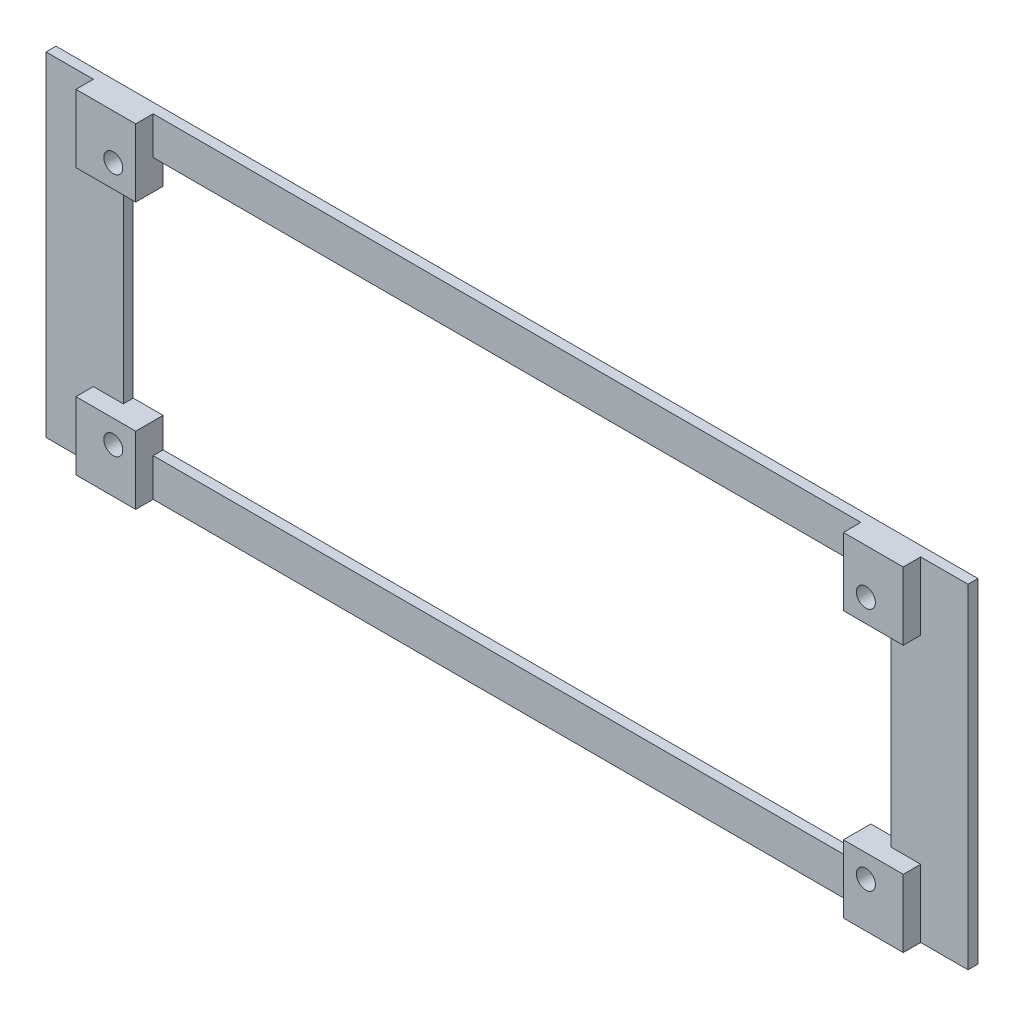
SolidWorks part; units mm, degrees
ref_plane "Přední rovina" through (0, 0, 0) normal (0, 0, 1) x (1, 0, 0)
ref_plane "Horní rovina" through (0, 0, 0) normal (0, 1, 0) x (1, 0, 0)
ref_plane "Pravá rovina" through (0, 0, 0) normal (1, 0, 0) x (0, 0, -1)
sketch "Skica1" plane through (0, 0, 0) normal (0, 0, 1) x (1, 0, 0)
  line L0 (-71, -25.9) -> (-71, -19.9)
  line L1 (-92.5, 33.5) -> (92.5, 33.5)
  line L2 (-92.5, 33.5) -> (-92.5, -33.5)
  line L3 (-92.5, -33.5) -> (92.5, -33.5)
  line L4 (92.5, 33.5) -> (92.5, -33.5)
  line L5 (-92.5, 33.5) -> (92.5, -33.5) construction
  line L6 (-92.5, -33.5) -> (92.5, 33.5) construction
  line L7 (-77, 25.9) -> (77, 25.9)
  line L8 (-77, 25.9) -> (-77, -25.9)
  line L9 (-77, -25.9) -> (77, -25.9)
  line L10 (77, 25.9) -> (77, -25.9)
  line L11 (-77, 25.9) -> (77, -25.9) construction
  line L12 (-77, -25.9) -> (77, 25.9) construction
  line L13 (-71, -19.9) -> (-77, -19.9)
  line L14 (0, 0) -> (0, -11.7122)
  line L15 (0, 0) -> (-11.7427, 0)
  line L16 (-71, 25.9) -> (-71, 19.9)
  line L17 (-71, 19.9) -> (-77, 19.9)
  line L18 (71, -25.9) -> (71, -19.9)
  line L19 (71, -19.9) -> (77, -19.9)
  line L20 (71, 25.9) -> (71, 19.9)
  line L21 (71, 19.9) -> (77, 19.9)
  point P0 (0, 0)
  point P6 (0, 0)
  dimension "D1" = 185
  dimension "D2" = 67
  dimension "D3" = 154
  dimension "D4" = 51.8
  dimension "D5" = 6
  dimension "D6" = 6
extrude "Přidat vysunutím1" add sketch "Skica1" along normal blind 2 contours L4 L1 L2 L3 L7 L10 L9 L8 | L17 L16 L7 L8 | L0 L13 L8 L9 | L19 L18 L9 L10 | L20 L21 L10 L7
sketch "Skica2" plane through (0, 0, 2) normal (0, 0, 1) x (1, 0, 0)
  line L0 (71, 19.9) -> (83, 19.9)
  line L1 (83, 19.9) -> (83, 33.5)
  line L2 (83, 33.5) -> (71, 33.5)
  line L3 (71, 33.5) -> (71, 19.9)
  line L4 (0, 0) -> (0, 13.6967)
  line L5 (0, 0) -> (-24.0722, 0)
  line L6 (-83, 33.5) -> (-71, 33.5)
  line L7 (-83, 19.9) -> (-83, 33.5)
  line L8 (-71, 33.5) -> (-71, 19.9)
  line L9 (-71, 19.9) -> (-83, 19.9)
  line L10 (-71, -19.9) -> (-83, -19.9)
  line L11 (-83, -19.9) -> (-83, -33.5)
  line L12 (-83, -33.5) -> (-71, -33.5)
  line L13 (-71, -33.5) -> (-71, -19.9)
  line L14 (71, -19.9) -> (83, -19.9)
  line L15 (71, -25.9) -> (71, -19.9)
  line L16 (83, -19.9) -> (83, -33.5)
  line L17 (-92.5, -33.5) -> (92.5, -33.5) construction
  line L18 (83, -33.5) -> (71, -33.5)
  line L19 (71, -33.5) -> (71, -19.9)
  line L20 (71, -19.9) -> (71.1065, -19.6847)
  dimension "D1" = 12
extrude "Přidat vysunutím2" add sketch "Skica2" along normal blind 3.5
sketch "Skica3" plane through (0, 0, 5.5) normal (0, 0, 1) x (1, 0, 0)
  line L1 (75.5, 24.5) -> (-75.5, 24.5)
  line L2 (75.5, 24.5) -> (75.5, -24.5)
  line L3 (75.5, -24.5) -> (-75.5, -24.5)
  line L4 (-75.5, 24.5) -> (-75.5, -24.5)
  line L5 (75.5, 24.5) -> (-75.5, -24.5) construction
  line L6 (75.5, -24.5) -> (-75.5, 24.5) construction
  point P0 (0, 0)
  dimension "D1" = 151
  dimension "D2" = 49
hole_wizard "Válcové zahloubení pro M3 šrouby s hlavou s vnitřním vybráním1" positions "Skica4" profile "Skica5" counterbore size "M3" standard "DIN" end condition through all
sketch "Skica4" plane through (0, 0, 5.5) normal (0, 0, 1) x (1, 0, 0)
  point P0 (75.5, -24.5)
  point P3 (75.5, 24.5)
  point P6 (-75.5, 24.5)
  point P9 (-75.5, -24.5)
sketch "Skica5" plane through (75.5, -24.5, 5.5) normal (1, 0, 0) x (0, -1, 0)
  line L0 (0, 0) -> (0, 5.5)
  line L1 (0, 5.5) -> (1.7, 5.5)
  line L3 (1.7, 5.5) -> (1.7, 4)
  line L4 (1.7, 4) -> (1.9, 4)
  line L5 (1.9, 4) -> (1.9, 0)
  line L7 (1.9, 0) -> (0, 0)
  line L11 (0, -6.35) -> (0, 107.95) construction
  dimension "Průměr díry skrz" = 3.4
  dimension "Hloubka díry skrz" = 5.5
  dimension "Průměr válcového zahloubení" = 3.8
  dimension "Hloubka válcového zahloubení" = 4
